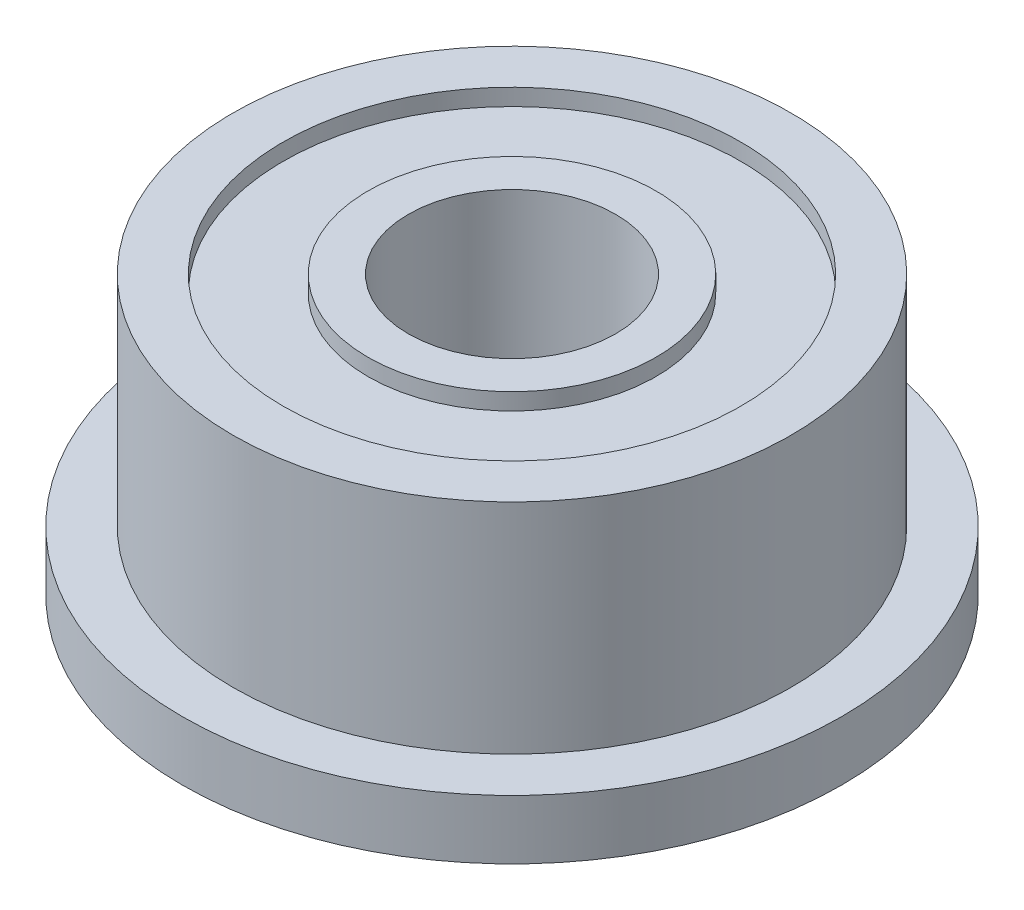
SolidWorks part; units mm, degrees
material "AISI 304"
ref_plane "Front Plane" through (0, 0, 0) normal (0, 0, 1) x (1, 0, 0)
ref_plane "Top Plane" through (0, 0, 0) normal (0, 1, 0) x (1, 0, 0)
ref_plane "Right Plane" through (0, 0, 0) normal (1, 0, 0) x (0, 0, -1)
ref_plane "Plane1" through (0, 0, 0) normal (0, 0, -1) x (-1, 0, 0)
sketch "Sketch1" plane through (0, 0, 0) normal (0, 0, -1) x (-1, 0, 0)
  line L0 (-2.065, 0.24) -> (-2.065, 0)
  line L1 (-2.065, 0) -> (-1.485, 0)
  line L2 (-1.485, 0) -> (-1.485, 3.98)
  line L3 (-1.485, 3.98) -> (-2.065, 3.98)
  line L4 (-2.065, 3.98) -> (-2.065, 3.74)
  line L5 (-2.065, 3.74) -> (-3.28, 3.74)
  line L6 (-3.28, 3.74) -> (-3.28, 3.98)
  line L7 (-3.28, 3.98) -> (-4, 3.98)
  line L8 (-4, 3.98) -> (-4, 0.85)
  line L9 (-4, 0.85) -> (-4.725, 0.85)
  line L10 (-4.725, 0.85) -> (-4.725, 0)
  line L11 (-4.725, 0) -> (-3.28, 0)
  line L12 (-3.28, 0) -> (-3.28, 0.24)
  line L13 (-3.28, 0.24) -> (-2.065, 0.24)
  line L14 (0, 0) -> (0, 3.98) construction
revolve "Revolve1" add sketch "Sketch1" angle 360 about L14
